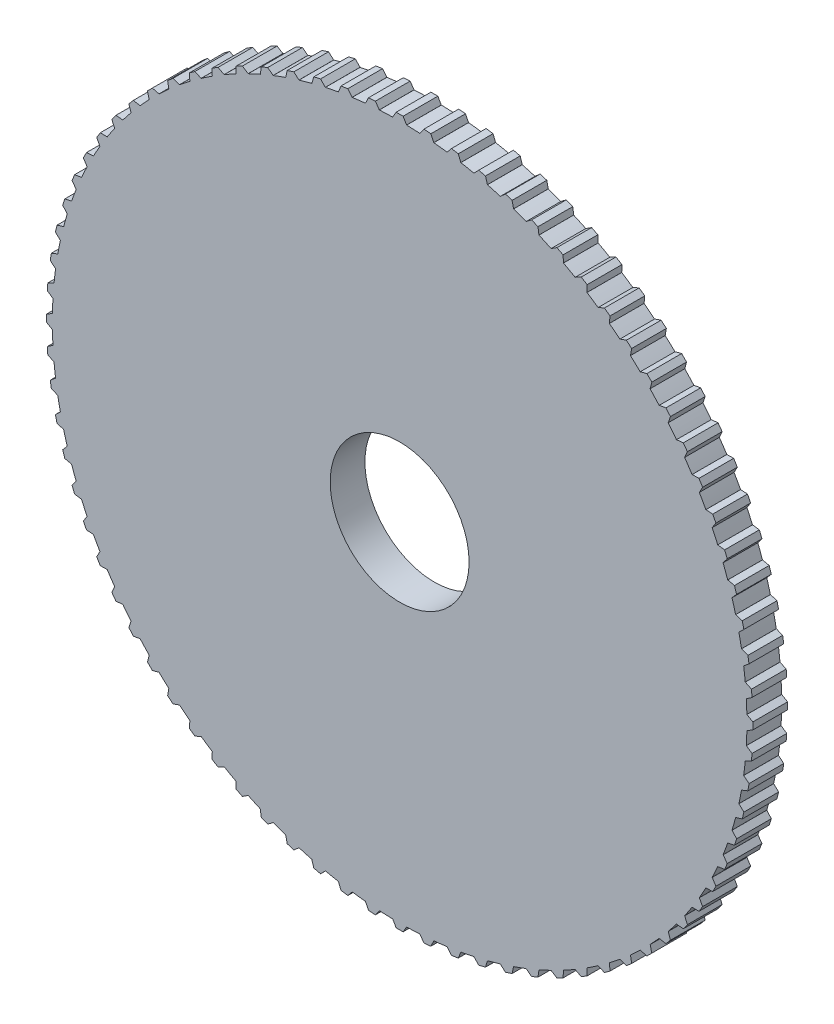
SolidWorks part; units mm, degrees
ref_plane "Front Plane" through (0, 0, 0) normal (0, 0, 1) x (1, 0, 0)
ref_plane "Top Plane" through (0, 0, 0) normal (0, 1, 0) x (1, 0, 0)
ref_plane "Right Plane" through (0, 0, 0) normal (1, 0, 0) x (0, 0, -1)
sketch "Sketch1" plane through (0, 0, 0) normal (0, 0, 1) x (1, 0, 0)
  line L1 (0, 101.7) -> (1, 101.7)
  line L2 (0, 101.7) -> (-1, 101.7)
  line L5 (-1, 101.7) -> (-2, 100)
  line L6 (1, 101.7) -> (2, 100)
  line L7 (-2, 100) -> (-1.9996, 99.98)
  line L8 (2, 100) -> (1.9996, 99.98)
  line L9 (6.9824, 101.465) -> (5.8521, 99.8487)
  line L10 (7.9793, 101.3865) -> (6.9824, 101.465)
  line L11 (7.9793, 101.3865) -> (8.9762, 101.308)
  line L12 (8.9762, 101.308) -> (9.8397, 99.5348)
  line L13 (5.8521, 99.8487) -> (5.8509, 99.8287)
  line L14 (9.8397, 99.5348) -> (9.8378, 99.5149)
  line L15 (14.9217, 100.6043) -> (13.6681, 99.0817)
  line L16 (15.9094, 100.4479) -> (14.9217, 100.6043)
  line L17 (15.9094, 100.4479) -> (16.8971, 100.2915)
  line L18 (16.8971, 100.2915) -> (17.6188, 98.456)
  line L19 (13.6681, 99.0817) -> (13.6653, 99.0619)
  line L20 (17.6188, 98.456) -> (17.6153, 98.4363)
  line L21 (22.769, 99.1235) -> (21.3998, 97.7039)
  line L22 (23.7414, 98.89) -> (22.769, 99.1235)
  line L23 (23.7414, 98.89) -> (24.7138, 98.6566)
  line L24 (24.7138, 98.6566) -> (25.2893, 96.7701)
  line L25 (21.3998, 97.7039) -> (21.3955, 97.6843)
  line L26 (25.2893, 96.7701) -> (25.2842, 96.7508)
  line L27 (30.476, 97.0315) -> (28.9996, 95.7237)
  line L28 (31.427, 96.7224) -> (30.476, 97.0315)
  line L29 (31.427, 96.7224) -> (32.3781, 96.4134)
  line L30 (32.3781, 96.4134) -> (32.8038, 94.4876)
  line L31 (28.9996, 95.7237) -> (28.9938, 95.7045)
  line L32 (32.8038, 94.4876) -> (32.7973, 94.4687)
  line L33 (37.995, 94.3412) -> (36.4206, 93.1533)
  line L34 (38.9189, 93.9585) -> (37.995, 94.3412)
  line L35 (38.9189, 93.9585) -> (39.8428, 93.5759)
  line L36 (39.8428, 93.5759) -> (40.1161, 91.6226)
  line L37 (36.4206, 93.1533) -> (36.4133, 93.1347)
  line L38 (40.1161, 91.6226) -> (40.1081, 91.6043)
  line L39 (45.2798, 91.0694) -> (43.617, 90.0086)
  line L40 (46.1708, 90.6154) -> (45.2798, 91.0694)
  line L41 (46.1708, 90.6154) -> (47.0618, 90.1614)
  line L42 (47.0618, 90.1614) -> (47.1811, 88.1927)
  line L43 (43.617, 90.0086) -> (43.6083, 89.9906)
  line L44 (47.1811, 88.1927) -> (47.1716, 88.175)
  line L45 (52.2855, 87.236) -> (50.5446, 86.309)
  line L46 (53.1381, 86.7135) -> (52.2855, 87.236)
  line L47 (53.1381, 86.7135) -> (53.9907, 86.191)
  line L48 (53.9907, 86.191) -> (53.9551, 84.219)
  line L49 (50.5446, 86.309) -> (50.5345, 86.2918)
  line L50 (53.9551, 84.219) -> (53.9443, 84.2022)
  line L51 (58.9687, 82.8648) -> (57.1605, 82.0773)
  line L52 (59.7778, 82.277) -> (58.9687, 82.8648)
  line L53 (59.7778, 82.277) -> (60.5868, 81.6892)
  line L54 (60.5868, 81.6892) -> (60.3966, 79.7261)
  line L55 (57.1605, 82.0773) -> (57.1491, 82.0609)
  line L56 (60.3966, 79.7261) -> (60.3845, 79.7102)
  line L57 (65.2885, 77.9827) -> (63.424, 77.3395)
  line L58 (66.0489, 77.3333) -> (65.2885, 77.9827)
  line L59 (66.0489, 77.3333) -> (66.8093, 76.6838)
  line L60 (66.8093, 76.6838) -> (66.4656, 74.7417)
  line L61 (63.424, 77.3395) -> (63.4113, 77.324)
  line L62 (66.4656, 74.7417) -> (66.4523, 74.7268)
  line L63 (71.2057, 72.6199) -> (69.2965, 72.1249)
  line L64 (71.9128, 71.9128) -> (71.2057, 72.6199)
  line L65 (71.9128, 71.9128) -> (72.6199, 71.2057)
  line L66 (72.6199, 71.2057) -> (72.1249, 69.2965)
  line L67 (69.2965, 72.1249) -> (69.2826, 72.1105)
  line L68 (72.1249, 69.2965) -> (72.1105, 69.2826)
  line L69 (76.6838, 66.8093) -> (74.7417, 66.4656)
  line L70 (77.3333, 66.0489) -> (76.6838, 66.8093)
  line L71 (77.3333, 66.0489) -> (77.9827, 65.2885)
  line L72 (77.9827, 65.2885) -> (77.3395, 63.424)
  line L73 (74.7417, 66.4656) -> (74.7268, 66.4523)
  line L74 (77.3395, 63.424) -> (77.324, 63.4113)
  line L75 (81.6892, 60.5868) -> (79.7261, 60.3966)
  line L76 (82.277, 59.7778) -> (81.6892, 60.5868)
  line L77 (82.277, 59.7778) -> (82.8648, 58.9687)
  line L78 (82.8648, 58.9687) -> (82.0773, 57.1605)
  line L79 (79.7261, 60.3966) -> (79.7102, 60.3845)
  line L80 (82.0773, 57.1605) -> (82.0609, 57.1491)
  line L81 (86.191, 53.9907) -> (84.219, 53.9551)
  line L82 (86.7135, 53.1381) -> (86.191, 53.9907)
  line L83 (86.7135, 53.1381) -> (87.236, 52.2855)
  line L84 (87.236, 52.2855) -> (86.309, 50.5446)
  line L85 (84.219, 53.9551) -> (84.2022, 53.9443)
  line L86 (86.309, 50.5446) -> (86.2918, 50.5345)
  line L87 (90.1614, 47.0618) -> (88.1927, 47.1811)
  line L88 (90.6154, 46.1708) -> (90.1614, 47.0618)
  line L89 (90.6154, 46.1708) -> (91.0694, 45.2798)
  line L90 (91.0694, 45.2798) -> (90.0086, 43.617)
  line L91 (88.1927, 47.1811) -> (88.175, 47.1716)
  line L92 (90.0086, 43.617) -> (89.9906, 43.6083)
  line L93 (93.5759, 39.8428) -> (91.6226, 40.1161)
  line L94 (93.9585, 38.9189) -> (93.5759, 39.8428)
  line L95 (93.9585, 38.9189) -> (94.3412, 37.995)
  line L96 (94.3412, 37.995) -> (93.1533, 36.4206)
  line L97 (91.6226, 40.1161) -> (91.6043, 40.1081)
  line L98 (93.1533, 36.4206) -> (93.1347, 36.4133)
  line L99 (96.4134, 32.3781) -> (94.4876, 32.8038)
  line L100 (96.7224, 31.427) -> (96.4134, 32.3781)
  line L101 (96.7224, 31.427) -> (97.0315, 30.476)
  line L102 (97.0315, 30.476) -> (95.7237, 28.9996)
  line L103 (94.4876, 32.8038) -> (94.4687, 32.7973)
  line L104 (95.7237, 28.9996) -> (95.7045, 28.9938)
  line L105 (98.6566, 24.7138) -> (96.7701, 25.2893)
  line L106 (98.89, 23.7414) -> (98.6566, 24.7138)
  line L107 (98.89, 23.7414) -> (99.1235, 22.769)
  line L108 (99.1235, 22.769) -> (97.7039, 21.3998)
  line L109 (96.7701, 25.2893) -> (96.7508, 25.2842)
  line L110 (97.7039, 21.3998) -> (97.6843, 21.3955)
  line L111 (100.2915, 16.8971) -> (98.456, 17.6188)
  line L112 (100.4479, 15.9094) -> (100.2915, 16.8971)
  line L113 (100.4479, 15.9094) -> (100.6043, 14.9217)
  line L114 (100.6043, 14.9217) -> (99.0817, 13.6681)
  line L115 (98.456, 17.6188) -> (98.4363, 17.6153)
  line L116 (99.0817, 13.6681) -> (99.0619, 13.6653)
  line L117 (101.308, 8.9762) -> (99.5348, 9.8397)
  line L118 (101.3865, 7.9793) -> (101.308, 8.9762)
  line L119 (101.3865, 7.9793) -> (101.465, 6.9824)
  line L120 (101.465, 6.9824) -> (99.8487, 5.8521)
  line L121 (99.5348, 9.8397) -> (99.5149, 9.8378)
  line L122 (99.8487, 5.8521) -> (99.8287, 5.8509)
  line L123 (101.7, 1) -> (100, 2)
  line L124 (101.7, 0) -> (101.7, 1)
  line L125 (101.7, 0) -> (101.7, -1)
  line L126 (101.7, -1) -> (100, -2)
  line L127 (100, 2) -> (99.98, 1.9996)
  line L128 (100, -2) -> (99.98, -1.9996)
  line L129 (101.465, -6.9824) -> (99.8487, -5.8521)
  line L130 (101.3865, -7.9793) -> (101.465, -6.9824)
  line L131 (101.3865, -7.9793) -> (101.308, -8.9762)
  line L132 (101.308, -8.9762) -> (99.5348, -9.8397)
  line L133 (99.8487, -5.8521) -> (99.8287, -5.8509)
  line L134 (99.5348, -9.8397) -> (99.5149, -9.8378)
  line L135 (100.6043, -14.9217) -> (99.0817, -13.6681)
  line L136 (100.4479, -15.9094) -> (100.6043, -14.9217)
  line L137 (100.4479, -15.9094) -> (100.2915, -16.8971)
  line L138 (100.2915, -16.8971) -> (98.456, -17.6188)
  line L139 (99.0817, -13.6681) -> (99.0619, -13.6653)
  line L140 (98.456, -17.6188) -> (98.4363, -17.6153)
  line L141 (99.1235, -22.769) -> (97.7039, -21.3998)
  line L142 (98.89, -23.7414) -> (99.1235, -22.769)
  line L143 (98.89, -23.7414) -> (98.6566, -24.7138)
  line L144 (98.6566, -24.7138) -> (96.7701, -25.2893)
  line L145 (97.7039, -21.3998) -> (97.6843, -21.3955)
  line L146 (96.7701, -25.2893) -> (96.7508, -25.2842)
  line L147 (97.0315, -30.476) -> (95.7237, -28.9996)
  line L148 (96.7224, -31.427) -> (97.0315, -30.476)
  line L149 (96.7224, -31.427) -> (96.4134, -32.3781)
  line L150 (96.4134, -32.3781) -> (94.4876, -32.8038)
  line L151 (95.7237, -28.9996) -> (95.7045, -28.9938)
  line L152 (94.4876, -32.8038) -> (94.4687, -32.7973)
  line L153 (94.3412, -37.995) -> (93.1533, -36.4206)
  line L154 (93.9585, -38.9189) -> (94.3412, -37.995)
  line L155 (93.9585, -38.9189) -> (93.5759, -39.8428)
  line L156 (93.5759, -39.8428) -> (91.6226, -40.1161)
  line L157 (93.1533, -36.4206) -> (93.1347, -36.4133)
  line L158 (91.6226, -40.1161) -> (91.6043, -40.1081)
  line L159 (91.0694, -45.2798) -> (90.0086, -43.617)
  line L160 (90.6154, -46.1708) -> (91.0694, -45.2798)
  line L161 (90.6154, -46.1708) -> (90.1614, -47.0618)
  line L162 (90.1614, -47.0618) -> (88.1927, -47.1811)
  line L163 (90.0086, -43.617) -> (89.9906, -43.6083)
  line L164 (88.1927, -47.1811) -> (88.175, -47.1716)
  line L165 (87.236, -52.2855) -> (86.309, -50.5446)
  line L166 (86.7135, -53.1381) -> (87.236, -52.2855)
  line L167 (86.7135, -53.1381) -> (86.191, -53.9907)
  line L168 (86.191, -53.9907) -> (84.219, -53.9551)
  line L169 (86.309, -50.5446) -> (86.2918, -50.5345)
  line L170 (84.219, -53.9551) -> (84.2022, -53.9443)
  line L171 (82.8648, -58.9687) -> (82.0773, -57.1605)
  line L172 (82.277, -59.7778) -> (82.8648, -58.9687)
  line L173 (82.277, -59.7778) -> (81.6892, -60.5868)
  line L174 (81.6892, -60.5868) -> (79.7261, -60.3966)
  line L175 (82.0773, -57.1605) -> (82.0609, -57.1491)
  line L176 (79.7261, -60.3966) -> (79.7102, -60.3845)
  line L177 (77.9827, -65.2885) -> (77.3395, -63.424)
  line L178 (77.3333, -66.0489) -> (77.9827, -65.2885)
  line L179 (77.3333, -66.0489) -> (76.6838, -66.8093)
  line L180 (76.6838, -66.8093) -> (74.7417, -66.4656)
  line L181 (77.3395, -63.424) -> (77.324, -63.4113)
  line L182 (74.7417, -66.4656) -> (74.7268, -66.4523)
  line L183 (72.6199, -71.2057) -> (72.1249, -69.2965)
  line L184 (71.9128, -71.9128) -> (72.6199, -71.2057)
  line L185 (71.9128, -71.9128) -> (71.2057, -72.6199)
  line L186 (71.2057, -72.6199) -> (69.2965, -72.1249)
  line L187 (72.1249, -69.2965) -> (72.1105, -69.2826)
  line L188 (69.2965, -72.1249) -> (69.2826, -72.1105)
  line L189 (66.8093, -76.6838) -> (66.4656, -74.7417)
  line L190 (66.0489, -77.3333) -> (66.8093, -76.6838)
  line L191 (66.0489, -77.3333) -> (65.2885, -77.9827)
  line L192 (65.2885, -77.9827) -> (63.424, -77.3395)
  line L193 (66.4656, -74.7417) -> (66.4523, -74.7268)
  line L194 (63.424, -77.3395) -> (63.4113, -77.324)
  line L195 (60.5868, -81.6892) -> (60.3966, -79.7261)
  line L196 (59.7778, -82.277) -> (60.5868, -81.6892)
  line L197 (59.7778, -82.277) -> (58.9687, -82.8648)
  line L198 (58.9687, -82.8648) -> (57.1605, -82.0773)
  line L199 (60.3966, -79.7261) -> (60.3845, -79.7102)
  line L200 (57.1605, -82.0773) -> (57.1491, -82.0609)
  line L201 (53.9907, -86.191) -> (53.9551, -84.219)
  line L202 (53.1381, -86.7135) -> (53.9907, -86.191)
  line L203 (53.1381, -86.7135) -> (52.2855, -87.236)
  line L204 (52.2855, -87.236) -> (50.5446, -86.309)
  line L205 (53.9551, -84.219) -> (53.9443, -84.2022)
  line L206 (50.5446, -86.309) -> (50.5345, -86.2918)
  line L207 (47.0618, -90.1614) -> (47.1811, -88.1927)
  line L208 (46.1708, -90.6154) -> (47.0618, -90.1614)
  line L209 (46.1708, -90.6154) -> (45.2798, -91.0694)
  line L210 (45.2798, -91.0694) -> (43.617, -90.0086)
  line L211 (47.1811, -88.1927) -> (47.1716, -88.175)
  line L212 (43.617, -90.0086) -> (43.6083, -89.9906)
  line L213 (39.8428, -93.5759) -> (40.1161, -91.6226)
  line L214 (38.9189, -93.9585) -> (39.8428, -93.5759)
  line L215 (38.9189, -93.9585) -> (37.995, -94.3412)
  line L216 (37.995, -94.3412) -> (36.4206, -93.1533)
  line L217 (40.1161, -91.6226) -> (40.1081, -91.6043)
  line L218 (36.4206, -93.1533) -> (36.4133, -93.1347)
  line L219 (32.3781, -96.4134) -> (32.8038, -94.4876)
  line L220 (31.427, -96.7224) -> (32.3781, -96.4134)
  line L221 (31.427, -96.7224) -> (30.476, -97.0315)
  line L222 (30.476, -97.0315) -> (28.9996, -95.7237)
  line L223 (32.8038, -94.4876) -> (32.7973, -94.4687)
  line L224 (28.9996, -95.7237) -> (28.9938, -95.7045)
  line L225 (24.7138, -98.6566) -> (25.2893, -96.7701)
  line L226 (23.7414, -98.89) -> (24.7138, -98.6566)
  line L227 (23.7414, -98.89) -> (22.769, -99.1235)
  line L228 (22.769, -99.1235) -> (21.3998, -97.7039)
  line L229 (25.2893, -96.7701) -> (25.2842, -96.7508)
  line L230 (21.3998, -97.7039) -> (21.3955, -97.6843)
  line L231 (16.8971, -100.2915) -> (17.6188, -98.456)
  line L232 (15.9094, -100.4479) -> (16.8971, -100.2915)
  line L233 (15.9094, -100.4479) -> (14.9217, -100.6043)
  line L234 (14.9217, -100.6043) -> (13.6681, -99.0817)
  line L235 (17.6188, -98.456) -> (17.6153, -98.4363)
  line L236 (13.6681, -99.0817) -> (13.6653, -99.0619)
  line L237 (8.9762, -101.308) -> (9.8397, -99.5348)
  line L238 (7.9793, -101.3865) -> (8.9762, -101.308)
  line L239 (7.9793, -101.3865) -> (6.9824, -101.465)
  line L240 (6.9824, -101.465) -> (5.8521, -99.8487)
  line L241 (9.8397, -99.5348) -> (9.8378, -99.5149)
  line L242 (5.8521, -99.8487) -> (5.8509, -99.8287)
  line L243 (1, -101.7) -> (2, -100)
  line L244 (0, -101.7) -> (1, -101.7)
  line L245 (0, -101.7) -> (-1, -101.7)
  line L246 (-1, -101.7) -> (-2, -100)
  line L247 (2, -100) -> (1.9996, -99.98)
  line L248 (-2, -100) -> (-1.9996, -99.98)
  line L249 (-6.9824, -101.465) -> (-5.8521, -99.8487)
  line L250 (-7.9793, -101.3865) -> (-6.9824, -101.465)
  line L251 (-7.9793, -101.3865) -> (-8.9762, -101.308)
  line L252 (-8.9762, -101.308) -> (-9.8397, -99.5348)
  line L253 (-5.8521, -99.8487) -> (-5.8509, -99.8287)
  line L254 (-9.8397, -99.5348) -> (-9.8378, -99.5149)
  line L255 (-14.9217, -100.6043) -> (-13.6681, -99.0817)
  line L256 (-15.9094, -100.4479) -> (-14.9217, -100.6043)
  line L257 (-15.9094, -100.4479) -> (-16.8971, -100.2915)
  line L258 (-16.8971, -100.2915) -> (-17.6188, -98.456)
  line L259 (-13.6681, -99.0817) -> (-13.6653, -99.0619)
  line L260 (-17.6188, -98.456) -> (-17.6153, -98.4363)
  line L261 (-22.769, -99.1235) -> (-21.3998, -97.7039)
  line L262 (-23.7414, -98.89) -> (-22.769, -99.1235)
  line L263 (-23.7414, -98.89) -> (-24.7138, -98.6566)
  line L264 (-24.7138, -98.6566) -> (-25.2893, -96.7701)
  line L265 (-21.3998, -97.7039) -> (-21.3955, -97.6843)
  line L266 (-25.2893, -96.7701) -> (-25.2842, -96.7508)
  line L267 (-30.476, -97.0315) -> (-28.9996, -95.7237)
  line L268 (-31.427, -96.7224) -> (-30.476, -97.0315)
  line L269 (-31.427, -96.7224) -> (-32.3781, -96.4134)
  line L270 (-32.3781, -96.4134) -> (-32.8038, -94.4876)
  line L271 (-28.9996, -95.7237) -> (-28.9938, -95.7045)
  line L272 (-32.8038, -94.4876) -> (-32.7973, -94.4687)
  line L273 (-37.995, -94.3412) -> (-36.4206, -93.1533)
  line L274 (-38.9189, -93.9585) -> (-37.995, -94.3412)
  line L275 (-38.9189, -93.9585) -> (-39.8428, -93.5759)
  line L276 (-39.8428, -93.5759) -> (-40.1161, -91.6226)
  line L277 (-36.4206, -93.1533) -> (-36.4133, -93.1347)
  line L278 (-40.1161, -91.6226) -> (-40.1081, -91.6043)
  line L279 (-45.2798, -91.0694) -> (-43.617, -90.0086)
  line L280 (-46.1708, -90.6154) -> (-45.2798, -91.0694)
  line L281 (-46.1708, -90.6154) -> (-47.0618, -90.1614)
  line L282 (-47.0618, -90.1614) -> (-47.1811, -88.1927)
  line L283 (-43.617, -90.0086) -> (-43.6083, -89.9906)
  line L284 (-47.1811, -88.1927) -> (-47.1716, -88.175)
  line L285 (-52.2855, -87.236) -> (-50.5446, -86.309)
  line L286 (-53.1381, -86.7135) -> (-52.2855, -87.236)
  line L287 (-53.1381, -86.7135) -> (-53.9907, -86.191)
  line L288 (-53.9907, -86.191) -> (-53.9551, -84.219)
  line L289 (-50.5446, -86.309) -> (-50.5345, -86.2918)
  line L290 (-53.9551, -84.219) -> (-53.9443, -84.2022)
  line L291 (-58.9687, -82.8648) -> (-57.1605, -82.0773)
  line L292 (-59.7778, -82.277) -> (-58.9687, -82.8648)
  line L293 (-59.7778, -82.277) -> (-60.5868, -81.6892)
  line L294 (-60.5868, -81.6892) -> (-60.3966, -79.7261)
  line L295 (-57.1605, -82.0773) -> (-57.1491, -82.0609)
  line L296 (-60.3966, -79.7261) -> (-60.3845, -79.7102)
  line L297 (-65.2885, -77.9827) -> (-63.424, -77.3395)
  line L298 (-66.0489, -77.3333) -> (-65.2885, -77.9827)
  line L299 (-66.0489, -77.3333) -> (-66.8093, -76.6838)
  line L300 (-66.8093, -76.6838) -> (-66.4656, -74.7417)
  line L301 (-63.424, -77.3395) -> (-63.4113, -77.324)
  line L302 (-66.4656, -74.7417) -> (-66.4523, -74.7268)
  line L303 (-71.2057, -72.6199) -> (-69.2965, -72.1249)
  line L304 (-71.9128, -71.9128) -> (-71.2057, -72.6199)
  line L305 (-71.9128, -71.9128) -> (-72.6199, -71.2057)
  line L306 (-72.6199, -71.2057) -> (-72.1249, -69.2965)
  line L307 (-69.2965, -72.1249) -> (-69.2826, -72.1105)
  line L308 (-72.1249, -69.2965) -> (-72.1105, -69.2826)
  line L309 (-76.6838, -66.8093) -> (-74.7417, -66.4656)
  line L310 (-77.3333, -66.0489) -> (-76.6838, -66.8093)
  line L311 (-77.3333, -66.0489) -> (-77.9827, -65.2885)
  line L312 (-77.9827, -65.2885) -> (-77.3395, -63.424)
  line L313 (-74.7417, -66.4656) -> (-74.7268, -66.4523)
  line L314 (-77.3395, -63.424) -> (-77.324, -63.4113)
  line L315 (-81.6892, -60.5868) -> (-79.7261, -60.3966)
  line L316 (-82.277, -59.7778) -> (-81.6892, -60.5868)
  line L317 (-82.277, -59.7778) -> (-82.8648, -58.9687)
  line L318 (-82.8648, -58.9687) -> (-82.0773, -57.1605)
  line L319 (-79.7261, -60.3966) -> (-79.7102, -60.3845)
  line L320 (-82.0773, -57.1605) -> (-82.0609, -57.1491)
  line L321 (-86.191, -53.9907) -> (-84.219, -53.9551)
  line L322 (-86.7135, -53.1381) -> (-86.191, -53.9907)
  line L323 (-86.7135, -53.1381) -> (-87.236, -52.2855)
  line L324 (-87.236, -52.2855) -> (-86.309, -50.5446)
  line L325 (-84.219, -53.9551) -> (-84.2022, -53.9443)
  line L326 (-86.309, -50.5446) -> (-86.2918, -50.5345)
  line L327 (-90.1614, -47.0618) -> (-88.1927, -47.1811)
  line L328 (-90.6154, -46.1708) -> (-90.1614, -47.0618)
  line L329 (-90.6154, -46.1708) -> (-91.0694, -45.2798)
  line L330 (-91.0694, -45.2798) -> (-90.0086, -43.617)
  line L331 (-88.1927, -47.1811) -> (-88.175, -47.1716)
  line L332 (-90.0086, -43.617) -> (-89.9906, -43.6083)
  line L333 (-93.5759, -39.8428) -> (-91.6226, -40.1161)
  line L334 (-93.9585, -38.9189) -> (-93.5759, -39.8428)
  line L335 (-93.9585, -38.9189) -> (-94.3412, -37.995)
  line L336 (-94.3412, -37.995) -> (-93.1533, -36.4206)
  line L337 (-91.6226, -40.1161) -> (-91.6043, -40.1081)
  line L338 (-93.1533, -36.4206) -> (-93.1347, -36.4133)
  line L339 (-96.4134, -32.3781) -> (-94.4876, -32.8038)
  line L340 (-96.7224, -31.427) -> (-96.4134, -32.3781)
  line L341 (-96.7224, -31.427) -> (-97.0315, -30.476)
  line L342 (-97.0315, -30.476) -> (-95.7237, -28.9996)
  line L343 (-94.4876, -32.8038) -> (-94.4687, -32.7973)
  line L344 (-95.7237, -28.9996) -> (-95.7045, -28.9938)
  line L345 (-98.6566, -24.7138) -> (-96.7701, -25.2893)
  line L346 (-98.89, -23.7414) -> (-98.6566, -24.7138)
  line L347 (-98.89, -23.7414) -> (-99.1235, -22.769)
  line L348 (-99.1235, -22.769) -> (-97.7039, -21.3998)
  line L349 (-96.7701, -25.2893) -> (-96.7508, -25.2842)
  line L350 (-97.7039, -21.3998) -> (-97.6843, -21.3955)
  line L351 (-100.2915, -16.8971) -> (-98.456, -17.6188)
  line L352 (-100.4479, -15.9094) -> (-100.2915, -16.8971)
  line L353 (-100.4479, -15.9094) -> (-100.6043, -14.9217)
  line L354 (-100.6043, -14.9217) -> (-99.0817, -13.6681)
  line L355 (-98.456, -17.6188) -> (-98.4363, -17.6153)
  line L356 (-99.0817, -13.6681) -> (-99.0619, -13.6653)
  line L357 (-101.308, -8.9762) -> (-99.5348, -9.8397)
  line L358 (-101.3865, -7.9793) -> (-101.308, -8.9762)
  line L359 (-101.3865, -7.9793) -> (-101.465, -6.9824)
  line L360 (-101.465, -6.9824) -> (-99.8487, -5.8521)
  line L361 (-99.5348, -9.8397) -> (-99.5149, -9.8378)
  line L362 (-99.8487, -5.8521) -> (-99.8287, -5.8509)
  line L363 (-101.7, -1) -> (-100, -2)
  line L364 (-101.7, 0) -> (-101.7, -1)
  line L365 (-101.7, 0) -> (-101.7, 1)
  line L366 (-101.7, 1) -> (-100, 2)
  line L367 (-100, -2) -> (-99.98, -1.9996)
  line L368 (-100, 2) -> (-99.98, 1.9996)
  line L369 (-101.465, 6.9824) -> (-99.8487, 5.8521)
  line L370 (-101.3865, 7.9793) -> (-101.465, 6.9824)
  line L371 (-101.3865, 7.9793) -> (-101.308, 8.9762)
  line L372 (-101.308, 8.9762) -> (-99.5348, 9.8397)
  line L373 (-99.8487, 5.8521) -> (-99.8287, 5.8509)
  line L374 (-99.5348, 9.8397) -> (-99.5149, 9.8378)
  line L375 (-100.6043, 14.9217) -> (-99.0817, 13.6681)
  line L376 (-100.4479, 15.9094) -> (-100.6043, 14.9217)
  line L377 (-100.4479, 15.9094) -> (-100.2915, 16.8971)
  line L378 (-100.2915, 16.8971) -> (-98.456, 17.6188)
  line L379 (-99.0817, 13.6681) -> (-99.0619, 13.6653)
  line L380 (-98.456, 17.6188) -> (-98.4363, 17.6153)
  line L381 (-99.1235, 22.769) -> (-97.7039, 21.3998)
  line L382 (-98.89, 23.7414) -> (-99.1235, 22.769)
  line L383 (-98.89, 23.7414) -> (-98.6566, 24.7138)
  line L384 (-98.6566, 24.7138) -> (-96.7701, 25.2893)
  line L385 (-97.7039, 21.3998) -> (-97.6843, 21.3955)
  line L386 (-96.7701, 25.2893) -> (-96.7508, 25.2842)
  line L387 (-97.0315, 30.476) -> (-95.7237, 28.9996)
  line L388 (-96.7224, 31.427) -> (-97.0315, 30.476)
  line L389 (-96.7224, 31.427) -> (-96.4134, 32.3781)
  line L390 (-96.4134, 32.3781) -> (-94.4876, 32.8038)
  line L391 (-95.7237, 28.9996) -> (-95.7045, 28.9938)
  line L392 (-94.4876, 32.8038) -> (-94.4687, 32.7973)
  line L393 (-94.3412, 37.995) -> (-93.1533, 36.4206)
  line L394 (-93.9585, 38.9189) -> (-94.3412, 37.995)
  line L395 (-93.9585, 38.9189) -> (-93.5759, 39.8428)
  line L396 (-93.5759, 39.8428) -> (-91.6226, 40.1161)
  line L397 (-93.1533, 36.4206) -> (-93.1347, 36.4133)
  line L398 (-91.6226, 40.1161) -> (-91.6043, 40.1081)
  line L399 (-91.0694, 45.2798) -> (-90.0086, 43.617)
  line L400 (-90.6154, 46.1708) -> (-91.0694, 45.2798)
  line L401 (-90.6154, 46.1708) -> (-90.1614, 47.0618)
  line L402 (-90.1614, 47.0618) -> (-88.1927, 47.1811)
  line L403 (-90.0086, 43.617) -> (-89.9906, 43.6083)
  line L404 (-88.1927, 47.1811) -> (-88.175, 47.1716)
  line L405 (-87.236, 52.2855) -> (-86.309, 50.5446)
  line L406 (-86.7135, 53.1381) -> (-87.236, 52.2855)
  line L407 (-86.7135, 53.1381) -> (-86.191, 53.9907)
  line L408 (-86.191, 53.9907) -> (-84.219, 53.9551)
  line L409 (-86.309, 50.5446) -> (-86.2918, 50.5345)
  line L410 (-84.219, 53.9551) -> (-84.2022, 53.9443)
  line L411 (-82.8648, 58.9687) -> (-82.0773, 57.1605)
  line L412 (-82.277, 59.7778) -> (-82.8648, 58.9687)
  line L413 (-82.277, 59.7778) -> (-81.6892, 60.5868)
  line L414 (-81.6892, 60.5868) -> (-79.7261, 60.3966)
  line L415 (-82.0773, 57.1605) -> (-82.0609, 57.1491)
  line L416 (-79.7261, 60.3966) -> (-79.7102, 60.3845)
  line L417 (-77.9827, 65.2885) -> (-77.3395, 63.424)
  line L418 (-77.3333, 66.0489) -> (-77.9827, 65.2885)
  line L419 (-77.3333, 66.0489) -> (-76.6838, 66.8093)
  line L420 (-76.6838, 66.8093) -> (-74.7417, 66.4656)
  line L421 (-77.3395, 63.424) -> (-77.324, 63.4113)
  line L422 (-74.7417, 66.4656) -> (-74.7268, 66.4523)
  line L423 (-72.6199, 71.2057) -> (-72.1249, 69.2965)
  line L424 (-71.9128, 71.9128) -> (-72.6199, 71.2057)
  line L425 (-71.9128, 71.9128) -> (-71.2057, 72.6199)
  line L426 (-71.2057, 72.6199) -> (-69.2965, 72.1249)
  line L427 (-72.1249, 69.2965) -> (-72.1105, 69.2826)
  line L428 (-69.2965, 72.1249) -> (-69.2826, 72.1105)
  line L429 (-66.8093, 76.6838) -> (-66.4656, 74.7417)
  line L430 (-66.0489, 77.3333) -> (-66.8093, 76.6838)
  line L431 (-66.0489, 77.3333) -> (-65.2885, 77.9827)
  line L432 (-65.2885, 77.9827) -> (-63.424, 77.3395)
  line L433 (-66.4656, 74.7417) -> (-66.4523, 74.7268)
  line L434 (-63.424, 77.3395) -> (-63.4113, 77.324)
  line L435 (-60.5868, 81.6892) -> (-60.3966, 79.7261)
  line L436 (-59.7778, 82.277) -> (-60.5868, 81.6892)
  line L437 (-59.7778, 82.277) -> (-58.9687, 82.8648)
  line L438 (-58.9687, 82.8648) -> (-57.1605, 82.0773)
  line L439 (-60.3966, 79.7261) -> (-60.3845, 79.7102)
  line L440 (-57.1605, 82.0773) -> (-57.1491, 82.0609)
  line L441 (-53.9907, 86.191) -> (-53.9551, 84.219)
  line L442 (-53.1381, 86.7135) -> (-53.9907, 86.191)
  line L443 (-53.1381, 86.7135) -> (-52.2855, 87.236)
  line L444 (-52.2855, 87.236) -> (-50.5446, 86.309)
  line L445 (-53.9551, 84.219) -> (-53.9443, 84.2022)
  line L446 (-50.5446, 86.309) -> (-50.5345, 86.2918)
  line L447 (-47.0618, 90.1614) -> (-47.1811, 88.1927)
  line L448 (-46.1708, 90.6154) -> (-47.0618, 90.1614)
  line L449 (-46.1708, 90.6154) -> (-45.2798, 91.0694)
  line L450 (-45.2798, 91.0694) -> (-43.617, 90.0086)
  line L451 (-47.1811, 88.1927) -> (-47.1716, 88.175)
  line L452 (-43.617, 90.0086) -> (-43.6083, 89.9906)
  line L453 (-39.8428, 93.5759) -> (-40.1161, 91.6226)
  line L454 (-38.9189, 93.9585) -> (-39.8428, 93.5759)
  line L455 (-38.9189, 93.9585) -> (-37.995, 94.3412)
  line L456 (-37.995, 94.3412) -> (-36.4206, 93.1533)
  line L457 (-40.1161, 91.6226) -> (-40.1081, 91.6043)
  line L458 (-36.4206, 93.1533) -> (-36.4133, 93.1347)
  line L459 (-32.3781, 96.4134) -> (-32.8038, 94.4876)
  line L460 (-31.427, 96.7224) -> (-32.3781, 96.4134)
  line L461 (-31.427, 96.7224) -> (-30.476, 97.0315)
  line L462 (-30.476, 97.0315) -> (-28.9996, 95.7237)
  line L463 (-32.8038, 94.4876) -> (-32.7973, 94.4687)
  line L464 (-28.9996, 95.7237) -> (-28.9938, 95.7045)
  line L465 (-24.7138, 98.6566) -> (-25.2893, 96.7701)
  line L466 (-23.7414, 98.89) -> (-24.7138, 98.6566)
  line L467 (-23.7414, 98.89) -> (-22.769, 99.1235)
  line L468 (-22.769, 99.1235) -> (-21.3998, 97.7039)
  line L469 (-25.2893, 96.7701) -> (-25.2842, 96.7508)
  line L470 (-21.3998, 97.7039) -> (-21.3955, 97.6843)
  line L471 (-16.8971, 100.2915) -> (-17.6188, 98.456)
  line L472 (-15.9094, 100.4479) -> (-16.8971, 100.2915)
  line L473 (-15.9094, 100.4479) -> (-14.9217, 100.6043)
  line L474 (-14.9217, 100.6043) -> (-13.6681, 99.0817)
  line L475 (-17.6188, 98.456) -> (-17.6153, 98.4363)
  line L476 (-13.6681, 99.0817) -> (-13.6653, 99.0619)
  line L477 (-8.9762, 101.308) -> (-9.8397, 99.5348)
  line L478 (-7.9793, 101.3865) -> (-8.9762, 101.308)
  line L479 (-7.9793, 101.3865) -> (-6.9824, 101.465)
  line L480 (-6.9824, 101.465) -> (-5.8521, 99.8487)
  line L481 (-9.8397, 99.5348) -> (-9.8378, 99.5149)
  line L482 (-5.8521, 99.8487) -> (-5.8509, 99.8287)
  arc A0 (-1.9996, 99.98) -> (-5.8509, 99.8287) centre (0, 0) ccw
  arc A1 (-9.8378, 99.5149) -> (-13.6653, 99.0619) centre (0, 0) ccw
  arc A2 (-17.6153, 98.4363) -> (-21.3955, 97.6843) centre (0, 0) ccw
  arc A3 (-25.2842, 96.7508) -> (-28.9938, 95.7045) centre (0, 0) ccw
  arc A4 (5.8509, 99.8287) -> (1.9996, 99.98) centre (0, 0) ccw
  arc A5 (13.6653, 99.0619) -> (9.8378, 99.5149) centre (0, 0) ccw
  arc A6 (50.5345, 86.2918) -> (47.1716, 88.175) centre (0, 0) ccw
  arc A7 (43.6083, 89.9906) -> (40.1081, 91.6043) centre (0, 0) ccw
  arc A8 (36.4133, 93.1347) -> (32.7973, 94.4687) centre (0, 0) ccw
  arc A9 (28.9938, 95.7045) -> (25.2842, 96.7508) centre (0, 0) ccw
  arc A10 (21.3955, 97.6843) -> (17.6153, 98.4363) centre (0, 0) ccw
  arc A11 (-99.0619, 13.6653) -> (-99.5149, 9.8378) centre (0, 0) ccw
  arc A12 (-97.6843, 21.3955) -> (-98.4363, 17.6153) centre (0, 0) ccw
  arc A13 (-95.7045, 28.9938) -> (-96.7508, 25.2842) centre (0, 0) ccw
  arc A14 (-93.1347, 36.4133) -> (-94.4687, 32.7973) centre (0, 0) ccw
  arc A15 (-89.9906, 43.6083) -> (-91.6043, 40.1081) centre (0, 0) ccw
  arc A16 (-86.2918, 50.5345) -> (-88.175, 47.1716) centre (0, 0) ccw
  arc A17 (-82.0609, 57.1491) -> (-84.2022, 53.9443) centre (0, 0) ccw
  arc A18 (-77.324, 63.4113) -> (-79.7102, 60.3845) centre (0, 0) ccw
  arc A19 (-72.1105, 69.2826) -> (-74.7268, 66.4523) centre (0, 0) ccw
  arc A20 (-66.4523, 74.7268) -> (-69.2826, 72.1105) centre (0, 0) ccw
  arc A21 (-60.3845, 79.7102) -> (-63.4113, 77.324) centre (0, 0) ccw
  arc A22 (-53.9443, 84.2022) -> (-57.1491, 82.0609) centre (0, 0) ccw
  arc A23 (-47.1716, 88.175) -> (-50.5345, 86.2918) centre (0, 0) ccw
  arc A24 (-40.1081, 91.6043) -> (-43.6083, 89.9906) centre (0, 0) ccw
  arc A25 (-32.7973, 94.4687) -> (-36.4133, 93.1347) centre (0, 0) ccw
  arc A26 (91.6043, 40.1081) -> (89.9906, 43.6083) centre (0, 0) ccw
  arc A27 (88.175, 47.1716) -> (86.2918, 50.5345) centre (0, 0) ccw
  arc A28 (84.2022, 53.9443) -> (82.0609, 57.1491) centre (0, 0) ccw
  arc A29 (74.7268, 66.4523) -> (72.1105, 69.2826) centre (0, 0) ccw
  arc A30 (69.2826, 72.1105) -> (66.4523, 74.7268) centre (0, 0) ccw
  arc A31 (63.4113, 77.324) -> (60.3845, 79.7102) centre (0, 0) ccw
  arc A32 (57.1491, 82.0609) -> (53.9443, 84.2022) centre (0, 0) ccw
  arc A33 (79.7102, 60.3845) -> (77.324, 63.4113) centre (0, 0) ccw
  arc A34 (94.4687, 32.7973) -> (93.1347, 36.4133) centre (0, 0) ccw
  arc A35 (93.1347, -36.4133) -> (94.4687, -32.7973) centre (0, 0) ccw
  arc A36 (95.7045, -28.9938) -> (96.7508, -25.2842) centre (0, 0) ccw
  arc A37 (97.6843, -21.3955) -> (98.4363, -17.6153) centre (0, 0) ccw
  arc A38 (99.0619, -13.6653) -> (99.5149, -9.8378) centre (0, 0) ccw
  arc A39 (96.7508, 25.2842) -> (95.7045, 28.9938) centre (0, 0) ccw
  arc A40 (98.4363, 17.6153) -> (97.6843, 21.3955) centre (0, 0) ccw
  arc A41 (99.5149, 9.8378) -> (99.0619, 13.6653) centre (0, 0) ccw
  arc A42 (99.98, 1.9996) -> (99.8287, 5.8509) centre (0, 0) ccw
  arc A43 (99.8287, -5.8509) -> (99.98, -1.9996) centre (0, 0) ccw
  arc A44 (-99.8287, 5.8509) -> (-99.98, 1.9996) centre (0, 0) ccw
  arc A45 (-99.98, -1.9996) -> (-99.8287, -5.8509) centre (0, 0) ccw
  arc A46 (-99.5149, -9.8378) -> (-99.0619, -13.6653) centre (0, 0) ccw
  arc A47 (-98.4363, -17.6153) -> (-97.6843, -21.3955) centre (0, 0) ccw
  arc A48 (-96.7508, -25.2842) -> (-95.7045, -28.9938) centre (0, 0) ccw
  arc A49 (-94.4687, -32.7973) -> (-93.1347, -36.4133) centre (0, 0) ccw
  arc A50 (-91.6043, -40.1081) -> (-89.9906, -43.6083) centre (0, 0) ccw
  arc A51 (-88.175, -47.1716) -> (-86.2918, -50.5345) centre (0, 0) ccw
  arc A52 (-84.2022, -53.9443) -> (-82.0609, -57.1491) centre (0, 0) ccw
  arc A53 (-79.7102, -60.3845) -> (-77.324, -63.4113) centre (0, 0) ccw
  arc A54 (-74.7268, -66.4523) -> (-72.1105, -69.2826) centre (0, 0) ccw
  arc A55 (-69.2826, -72.1105) -> (-66.4523, -74.7268) centre (0, 0) ccw
  arc A56 (-63.4113, -77.324) -> (-60.3845, -79.7102) centre (0, 0) ccw
  arc A57 (-57.1491, -82.0609) -> (-53.9443, -84.2022) centre (0, 0) ccw
  arc A58 (-50.5345, -86.2918) -> (-47.1716, -88.175) centre (0, 0) ccw
  arc A59 (-43.6083, -89.9906) -> (-40.1081, -91.6043) centre (0, 0) ccw
  arc A60 (-36.4133, -93.1347) -> (-32.7973, -94.4687) centre (0, 0) ccw
  arc A61 (-28.9938, -95.7045) -> (-25.2842, -96.7508) centre (0, 0) ccw
  arc A62 (-21.3955, -97.6843) -> (-17.6153, -98.4363) centre (0, 0) ccw
  arc A63 (-13.6653, -99.0619) -> (-9.8378, -99.5149) centre (0, 0) ccw
  arc A64 (-5.8509, -99.8287) -> (-1.9996, -99.98) centre (0, 0) ccw
  arc A65 (1.9996, -99.98) -> (5.8509, -99.8287) centre (0, 0) ccw
  arc A66 (9.8378, -99.5149) -> (13.6653, -99.0619) centre (0, 0) ccw
  arc A67 (17.6153, -98.4363) -> (21.3955, -97.6843) centre (0, 0) ccw
  arc A68 (25.2842, -96.7508) -> (28.9938, -95.7045) centre (0, 0) ccw
  arc A69 (89.9906, -43.6083) -> (91.6043, -40.1081) centre (0, 0) ccw
  arc A70 (86.2918, -50.5345) -> (88.175, -47.1716) centre (0, 0) ccw
  arc A71 (82.0609, -57.1491) -> (84.2022, -53.9443) centre (0, 0) ccw
  arc A72 (77.324, -63.4113) -> (79.7102, -60.3845) centre (0, 0) ccw
  arc A73 (72.1105, -69.2826) -> (74.7268, -66.4523) centre (0, 0) ccw
  arc A74 (66.4523, -74.7268) -> (69.2826, -72.1105) centre (0, 0) ccw
  arc A75 (60.3845, -79.7102) -> (63.4113, -77.324) centre (0, 0) ccw
  arc A76 (53.9443, -84.2022) -> (57.1491, -82.0609) centre (0, 0) ccw
  arc A77 (47.1716, -88.175) -> (50.5345, -86.2918) centre (0, 0) ccw
  arc A78 (40.1081, -91.6043) -> (43.6083, -89.9906) centre (0, 0) ccw
  arc A79 (32.7973, -94.4687) -> (36.4133, -93.1347) centre (0, 0) ccw
  circle A80 centre (0, 0) radius 20
  point P407 (0, 0)
  dimension "D6" = 200
  dimension "D2" = 1
  dimension "D3" = 1
  dimension "D7" = 80
extrude "Boss-Extrude1" add sketch "Sketch1" along normal blind 10
